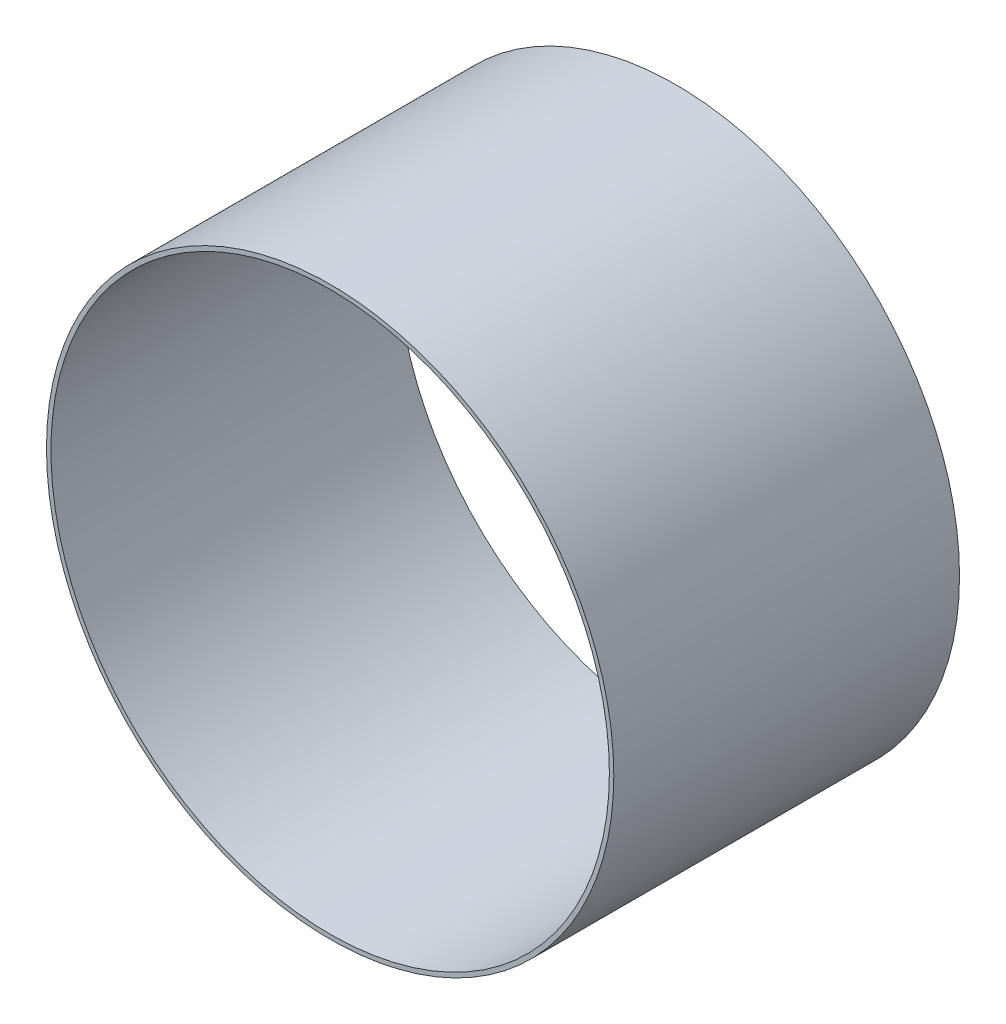
SolidWorks part; units mm, degrees
material "3.0205 (EN-AW 1200)"
ref_plane "Alzado" through (0, 0, 0) normal (0, 0, 1) x (1, 0, 0)
ref_plane "Planta" through (0, 0, 0) normal (0, 1, 0) x (1, 0, 0)
ref_plane "Vista lateral" through (0, 0, 0) normal (1, 0, 0) x (0, 0, -1)
sketch "Croquis1" plane through (0, 0, 0) normal (0, 0, 1) x (1, 0, 0)
  circle A0 centre (0, 0) radius 12.8
  circle A1 centre (0, 0) radius 12.6
  circle A2 centre (0, 0) radius 12.8 construction
  dimension "D2" = 0.2
extrude "Saliente-Extruir1" add sketch "Croquis1" along normal up to surface (15.6 mm away)
